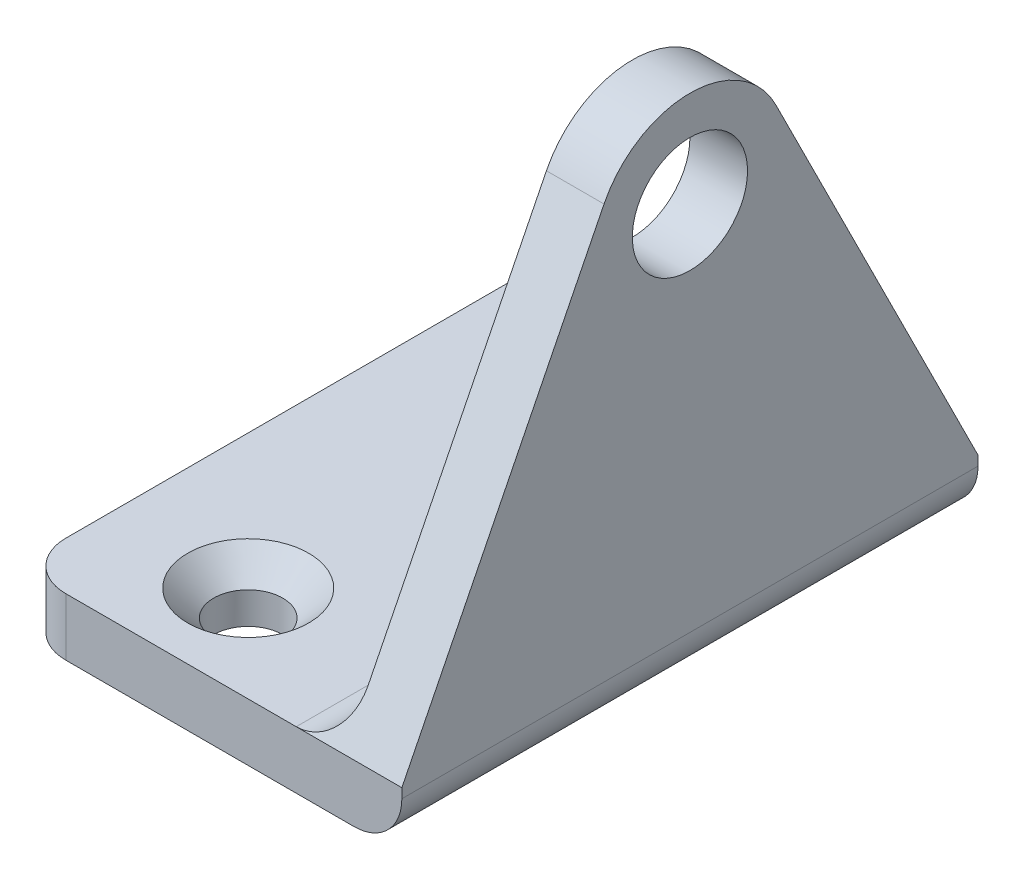
SolidWorks part; units mm, degrees
ref_plane "Front Plane" through (0, 0, 0) normal (0, 0, 1) x (1, 0, 0)
ref_plane "Top Plane" through (0, 0, 0) normal (0, 1, 0) x (1, 0, 0)
ref_plane "Right Plane" through (0, 0, 0) normal (1, 0, 0) x (0, 0, -1)
sketch "Sketch1" plane through (0, 0, 0) normal (0, 1, 0) x (1, 0, 0)
  line L1 (10, 15) -> (-10, 15)
  line L2 (10, 15) -> (10, -15)
  line L3 (10, -15) -> (-10, -15)
  line L4 (-10, 15) -> (-10, -15)
  line L5 (10, 15) -> (-10, -15) construction
  line L6 (10, -15) -> (-10, 15) construction
  point P0 (0, 0)
  point P10 (0, 0)
  dimension "D1" = 30
  dimension "D2" = 20
extrude "Boss-Extrude1" add sketch "Sketch1" along normal blind 3
sketch "Sketch3" plane through (10, 0, 0) normal (1, 0, 0) x (0, 0, -1)
  line L0 (-15, 3) -> (-4.4721, 24.0557)
  line L1 (4.4721, 24.0557) -> (15, 3)
  line L2 (-15, 3) -> (15, 3) construction
  arc A0 (-4.4721, 24.0557) -> (4.4721, 24.0557) centre (0, 21.8197) cw
  circle A1 centre (0, 21.8197) radius 3
  point P9 (0, 33)
  point P11 (0, 0)
  point P12 (0, 0)
  line M4 (15, 3) -> (-15, 3)
  dimension "D2" = 5
  dimension "D3" = 6
  dimension "D1" = 30
extrude "Boss-Extrude2" add sketch "Sketch3" against normal blind 3 contours A0 L0 L1 A1 M4
fillet "Fillet1" radius 2.5 3 edges at (-10, 1.5, -15) (-10, 1.5, 15) (10, 0, 0)
hole_wizard "CSK for M3 Flat Head Machine Screw1" positions "Sketch6" profile "Sketch5" countersink size "M3" standard "ANSI Metric"
sketch "Sketch6" plane through (0, 3, 0) normal (0, 1, 0) x (1, 0, 0)
  point P0 (-3, 10)
  point P4 (-3, -10)
  point P7 (0, 0)
  dimension "D1" = 10
  dimension "D2" = 3
  dimension "D3" = 10
sketch "Sketch5" plane through (-3, 3, -10) normal (1, 0, 0) x (0, 0, 1)
  line L0 (0, 0) -> (0, 6.0815)
  line L1 (0, 6.0815) -> (1.8, 5)
  line L2 (1.8, 5) -> (1.8, 1.35)
  line L3 (1.8, 1.35) -> (3.15, 0)
  line L5 (3.15, 0) -> (0, 0)
  line L6 (-1.8, 1.35) -> (-3.15, 0) construction
  line L10 (0, 6.0815) -> (-1.8, 5) construction
  line L11 (0, -6.35) -> (0, 107.95) construction
  dimension "Hole Dia." = 3.6
  dimension "Hole Depth" = 5
  dimension "Near C'Sink Dia." = 6.3
  dimension "Near C'Sink Angle" = 90
  dimension "Drill Angle" = 118
sketch "Sketch7" plane through (0, 3, 0) normal (0, 1, 0) x (1, 0, 0)
  line L0 (7, 15) -> (7, -15) construction
  line L1 (7, 2) -> (0, 2)
  line L2 (7, 2) -> (7, -2)
  line L3 (7, -2) -> (0, -2)
  arc A0 (0, 2) -> (0, -2) centre (0, 0) ccw
  dimension "D1" = 7
  dimension "D2" = 4
fillet "Fillet2" radius 2.5 1 edges at (7, 3, 0)
